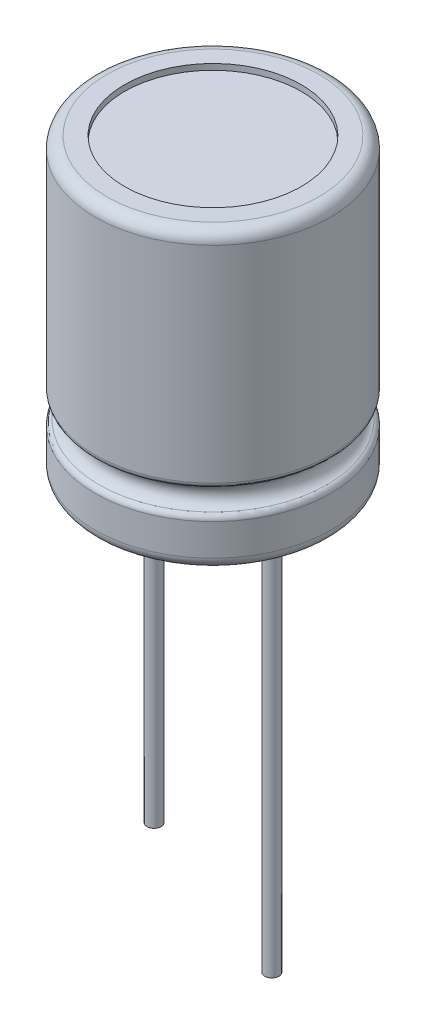
SolidWorks part; units mm, degrees
ref_plane "Front" through (0, 0, 0) normal (0, 0, 1) x (1, 0, 0)
ref_plane "Top" through (0, 0, 0) normal (0, 1, 0) x (1, 0, 0)
ref_plane "Right" through (0, 0, 0) normal (1, 0, 0) x (0, 0, -1)
sketch "Sketch1" plane through (0, 0, 0) normal (0, 1, 0) x (1, 0, 0)
  circle A0 centre (0, 0) radius 5
  dimension "D1" = 10
extrude "Base-Extrude" add sketch "Sketch1" along normal blind 12.5
sketch "Sketch2" plane through (0, 0, 0) normal (1, 0, 0) x (0, 0, -1)
  line L0 (-5, 12.5) -> (-5, 0) construction
  line L1 (-5, 3.0532) -> (-5, 2.0532)
  line L2 (0, 0) -> (0, 7.7627) construction
  line L3 (0, 12.5) -> (0, 0) construction
  arc A0 (-5, 2.0532) -> (-5, 3.0532) centre (-5, 2.5532) ccw
  dimension "D1" = 0.5
revolve "Cut-Revolve1" cut sketch "Sketch2" angle 360 about L2
fillet "Fillet1" radius 0.5 2 edges at (0, 0, 5) (0, 12.5, 5)
fillet "Fillet2" radius 0.25 2 edges at (0, 2.0532, -5) (0, 3.0532, -5)
sketch "Sketch4" plane through (0, 0, 0) normal (0, -1, 0) x (1, 0, 0)
  circle A0 centre (0, 0) radius 3.75
  dimension "D1" = 7.5
extrude "Cut-Extrude1" cut sketch "Sketch4" against normal blind 0.25
sketch "Sketch3" plane through (0, 0.25, 0) normal (0, -1, 0) x (1, 0, 0)
  circle A0 centre (-2.5, 0) radius 0.3
  circle A1 centre (2.5, 0) radius 0.3
  dimension "D1" = 0.6
  dimension "D2" = 2.5
  dimension "D3" = 5
extrude "Boss-Extrude1" add sketch "Sketch3" along normal blind 17.25
sketch "Sketch5" plane through (0, -17, 0) normal (0, -1, 0) x (1, 0, 0)
  circle A1 centre (-2.5, 0) radius 0.3
  circle A2 centre (-2.5, 0) radius 0.3
  dimension "D1" = 0
extrude "Cut-Extrude2" cut sketch "Sketch5" against normal blind 3
sketch "Sketch6" plane through (0, 12.5, 0) normal (0, 1, 0) x (-1, 0, 0)
  circle A0 centre (0, 0) radius 3.75
  dimension "D1" = 7.5
extrude "Cut-Extrude3" cut sketch "Sketch6" against normal blind 0.25
